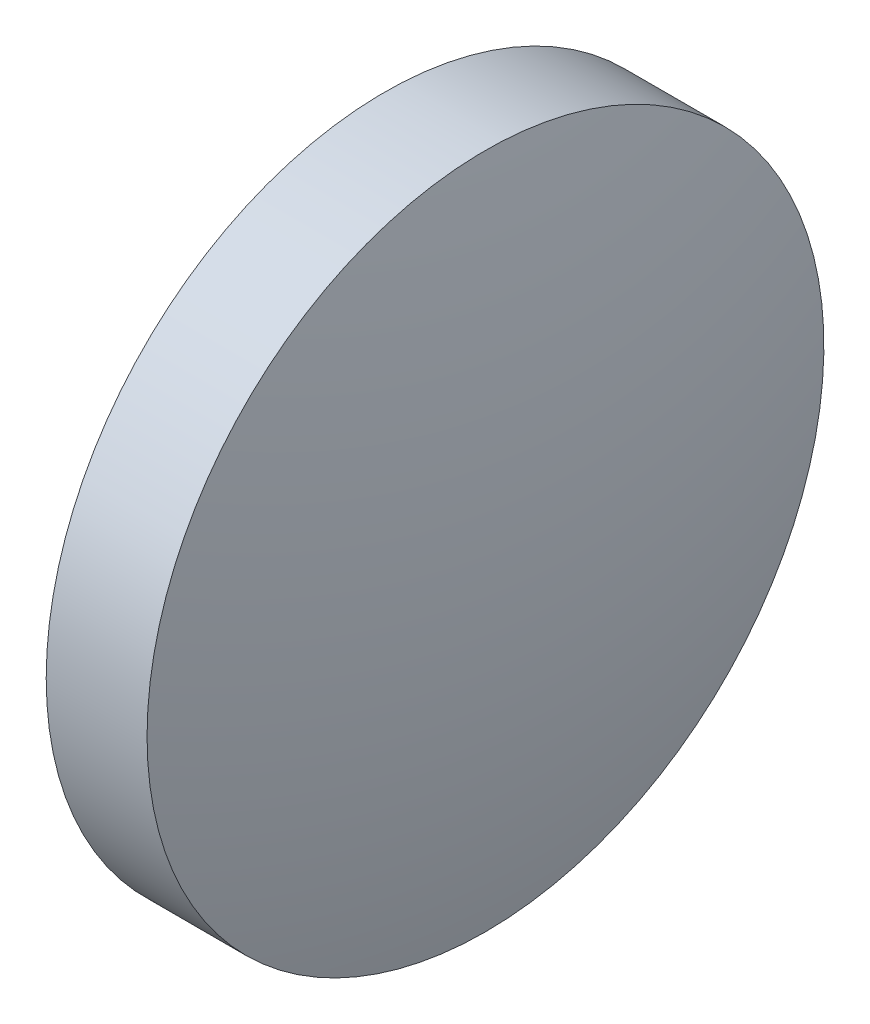
SolidWorks part; units mm, degrees
ref_plane "前视基准面" through (0, 0, 0) normal (0, 0, 1) x (1, 0, 0)
ref_plane "上视基准面" through (0, 0, 0) normal (0, 1, 0) x (1, 0, 0)
ref_plane "右视基准面" through (0, 0, 0) normal (1, 0, 0) x (0, 0, -1)
sketch "草图1" plane through (0, 0, 0) normal (0, 0, 1) x (1, 0, 0)
  line L0 (505.9054, 24.7489) -> (512.0408, 24.7489) construction
  line L1 (506.8469, 24.7489) -> (506.8469, 29.7489)
  line L2 (508.9731, 24.7489) -> (506.8469, 24.7489)
  line L5 (506.8469, 29.7489) -> (508.3369, 29.7489)
  arc A0 (508.9731, 24.7489) -> (508.3369, 29.7489) centre (489.0055, 24.7489) ccw
revolve "旋转1" add sketch "草图1" angle 360 about L0
